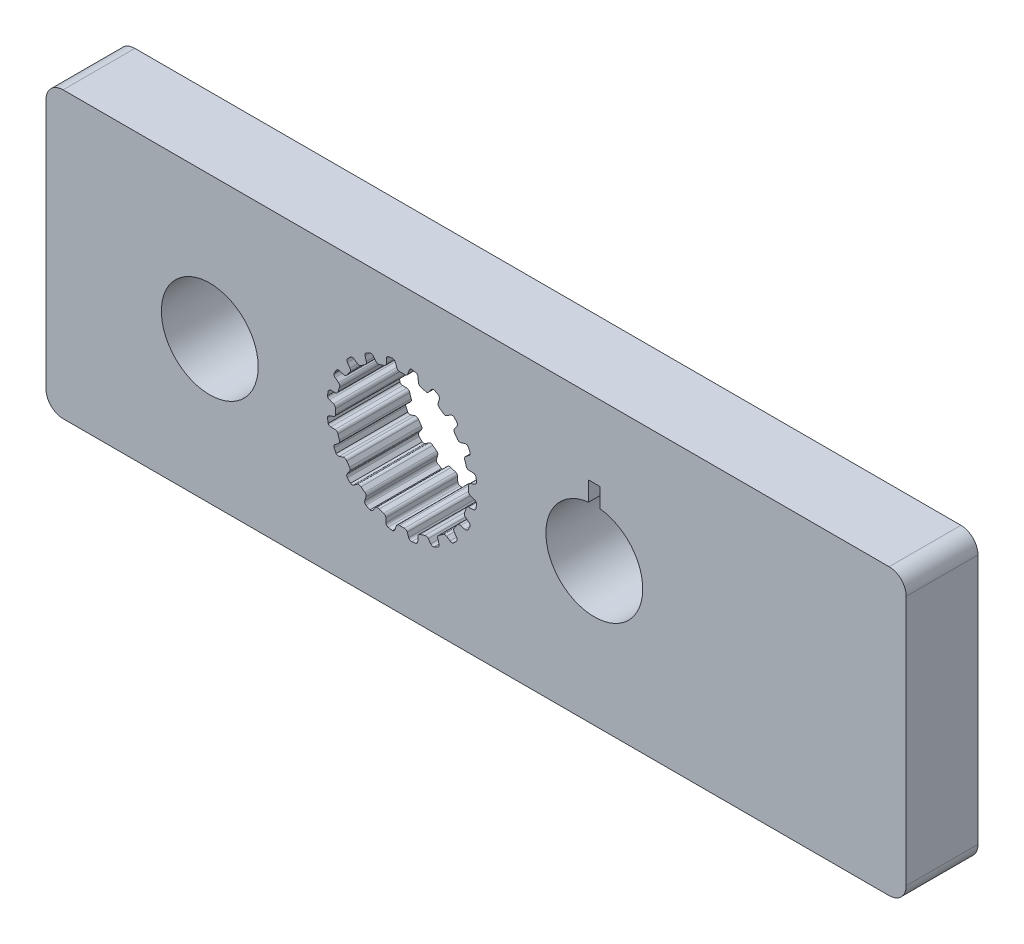
SolidWorks part; units mm, degrees
ref_plane "Front Plane" through (0, 0, 0) normal (0, 0, 1) x (1, 0, 0)
ref_plane "Top Plane" through (0, 0, 0) normal (0, 1, 0) x (1, 0, 0)
ref_plane "Right Plane" through (0, 0, 0) normal (1, 0, 0) x (0, 0, -1)
sketch "Sketch1" plane through (0, 0, 0) normal (0, 0, 1) x (1, 0, 0)
  line L0 (-0.1069, 2.9699) -> (0.1069, 2.9699)
  line L1 (0.3159, 3.2375) -> (0.2537, 3.0575)
  line L2 (-0.2964, 3.2367) -> (-0.2318, 3.0575)
  line L3 (-0.2964, 3.2367) -> (0.3159, 3.2375) construction
  line L4 (0, 3.3252) -> (0, 0) construction
  line L5 (-0.2318, 3.0575) -> (0.2537, 3.0575) construction
  line L6 (-0.4281, 3.3241) -> (0.4281, 3.3263) construction
  line L7 (0.7183, 3.1698) -> (0.7244, 2.9795)
  line L8 (0.816, 2.8576) -> (1.0195, 2.7915)
  line L9 (1.3009, 2.9815) -> (1.1862, 2.8295)
  line L10 (1.6627, 2.7927) -> (1.6097, 2.6099)
  line L11 (1.6591, 2.4655) -> (1.8322, 2.3398)
  line L12 (2.1585, 2.4335) -> (2.0025, 2.3245)
  line L13 (2.4443, 2.1423) -> (2.3374, 1.9847)
  line L14 (2.3398, 1.8322) -> (2.4655, 1.6591)
  line L15 (2.8049, 1.6474) -> (2.6228, 1.5919)
  line L16 (2.9866, 1.2821) -> (2.8363, 1.1653)
  line L17 (2.7915, 1.0195) -> (2.8576, 0.816)
  line L18 (3.1767, 0.7) -> (2.9863, 0.7035)
  line L19 (3.2367, 0.2964) -> (3.0575, 0.2318)
  line L20 (2.9699, 0.1069) -> (2.9699, -0.1069)
  line L21 (3.2375, -0.3159) -> (3.0575, -0.2537)
  line L22 (3.1698, -0.7183) -> (2.9795, -0.7244)
  line L23 (2.8576, -0.816) -> (2.7915, -1.0195)
  line L24 (2.9815, -1.3009) -> (2.8295, -1.1862)
  line L25 (2.7927, -1.6627) -> (2.6099, -1.6097)
  line L26 (2.4655, -1.6591) -> (2.3398, -1.8322)
  line L27 (2.4335, -2.1585) -> (2.3245, -2.0025)
  line L28 (2.1423, -2.4443) -> (1.9847, -2.3374)
  line L29 (1.8322, -2.3398) -> (1.6591, -2.4655)
  line L30 (1.6474, -2.8049) -> (1.5919, -2.6228)
  line L31 (1.2821, -2.9866) -> (1.1653, -2.8363)
  line L32 (1.0195, -2.7915) -> (0.816, -2.8576)
  line L33 (0.7, -3.1767) -> (0.7035, -2.9863)
  line L34 (0.2964, -3.2367) -> (0.2318, -3.0575)
  line L35 (0.1069, -2.9699) -> (-0.1069, -2.9699)
  line L36 (-0.3159, -3.2375) -> (-0.2537, -3.0575)
  line L37 (-0.7183, -3.1698) -> (-0.7244, -2.9795)
  line L38 (-0.816, -2.8576) -> (-1.0195, -2.7915)
  line L39 (-1.3009, -2.9815) -> (-1.1862, -2.8295)
  line L40 (-1.6627, -2.7927) -> (-1.6097, -2.6099)
  line L41 (-1.6591, -2.4655) -> (-1.8322, -2.3398)
  line L42 (-2.1585, -2.4335) -> (-2.0025, -2.3245)
  line L43 (-2.4443, -2.1423) -> (-2.3374, -1.9847)
  line L44 (-2.3398, -1.8322) -> (-2.4655, -1.6591)
  line L45 (-2.8049, -1.6474) -> (-2.6228, -1.5919)
  line L46 (-2.9866, -1.2821) -> (-2.8363, -1.1653)
  line L47 (-2.7915, -1.0195) -> (-2.8576, -0.816)
  line L48 (-3.1767, -0.7) -> (-2.9863, -0.7035)
  line L49 (-3.2367, -0.2964) -> (-3.0575, -0.2318)
  line L50 (-2.9699, -0.1069) -> (-2.9699, 0.1069)
  line L51 (-3.2375, 0.3159) -> (-3.0575, 0.2537)
  line L52 (-3.1698, 0.7183) -> (-2.9795, 0.7244)
  line L53 (-2.8576, 0.816) -> (-2.7915, 1.0195)
  line L54 (-2.9815, 1.3009) -> (-2.8295, 1.1862)
  line L55 (-2.7927, 1.6627) -> (-2.6099, 1.6097)
  line L56 (-2.4655, 1.6591) -> (-2.3398, 1.8322)
  line L57 (-2.4335, 2.1585) -> (-2.3245, 2.0025)
  line L58 (-2.1423, 2.4443) -> (-1.9847, 2.3374)
  line L59 (-1.8322, 2.3398) -> (-1.6591, 2.4655)
  line L60 (-1.6474, 2.8049) -> (-1.5919, 2.6228)
  line L61 (-1.2821, 2.9866) -> (-1.1653, 2.8363)
  line L62 (-1.0195, 2.7915) -> (-0.816, 2.8576)
  line L63 (-0.7, 3.1767) -> (-0.7035, 2.9863)
  line L64 (0.4281, 3.3263) -> (0.62, 3.2938)
  line L65 (1.4351, 3.0312) -> (1.6075, 2.9409)
  line L66 (2.3015, 2.4394) -> (2.4376, 2.3003)
  line L67 (2.9427, 1.6088) -> (3.0291, 1.4344)
  line L68 (3.2958, 0.6207) -> (3.3241, 0.4281)
  line L69 (3.3263, -0.4281) -> (3.2938, -0.62)
  line L70 (3.0312, -1.4351) -> (2.9409, -1.6075)
  line L71 (2.4394, -2.3015) -> (2.3003, -2.4376)
  line L72 (1.6088, -2.9427) -> (1.4344, -3.0291)
  line L73 (0.6207, -3.2958) -> (0.4281, -3.3241)
  line L74 (-0.4281, -3.3263) -> (-0.62, -3.2938)
  line L75 (-1.4351, -3.0312) -> (-1.6075, -2.9409)
  line L76 (-2.3015, -2.4394) -> (-2.4376, -2.3003)
  line L77 (-2.9427, -1.6088) -> (-3.0291, -1.4344)
  line L78 (-3.2958, -0.6207) -> (-3.3241, -0.4281)
  line L79 (-3.3263, 0.4281) -> (-3.2938, 0.62)
  line L80 (-3.0312, 1.4351) -> (-2.9409, 1.6075)
  line L81 (-2.4394, 2.3015) -> (-2.3003, 2.4376)
  line L82 (-1.6088, 2.9427) -> (-1.4344, 3.0291)
  line L83 (-0.6207, 3.2958) -> (-0.4281, 3.3241)
  line L84 (0, 0) -> (0, -6.35) construction
  line L85 (-15.875, 6.35) -> (22.479, 6.35)
  line L86 (-15.875, 6.35) -> (-15.875, -6.35)
  line L87 (-15.875, -6.35) -> (22.479, -6.35)
  line L88 (22.479, 6.35) -> (22.479, -6.35)
  line L89 (-8.5725, 0) -> (8.5725, 0) construction
  arc A0 (0.2537, 3.0575) -> (0.1069, 2.9699) centre (0.1283, 3.1009) cw
  arc A1 (-0.2318, 3.0575) -> (-0.1069, 2.9699) centre (-0.1069, 3.1026) ccw
  arc A2 (0.62, 3.2938) -> (0.7183, 3.1698) centre (0.5856, 3.1656) cw
  arc A3 (0.7244, 2.9795) -> (0.816, 2.8576) centre (0.857, 2.9838) ccw
  arc A4 (-0.4281, 3.3241) -> (-0.2964, 3.2367) centre (-0.4213, 3.1916) cw
  arc A5 (0.4281, 3.3263) -> (0.3159, 3.2375) centre (0.4413, 3.1942) ccw
  arc A6 (1.1862, 2.8295) -> (1.0195, 2.7915) centre (1.0802, 2.9095) cw
  arc A7 (1.4351, 3.0312) -> (1.3009, 2.9815) centre (1.4068, 2.9015) ccw
  arc A8 (1.6075, 2.9409) -> (1.6627, 2.7927) centre (1.5352, 2.8297) cw
  arc A9 (1.6097, 2.6099) -> (1.6591, 2.4655) centre (1.7371, 2.5729) ccw
  arc A10 (2.0025, 2.3245) -> (1.8322, 2.3398) centre (1.9264, 2.4332) cw
  arc A11 (2.3015, 2.4394) -> (2.1585, 2.4335) centre (2.2346, 2.3248) ccw
  arc A12 (2.4376, 2.3003) -> (2.4443, 2.1423) centre (2.3345, 2.2168) cw
  arc A13 (2.3374, 1.9847) -> (2.3398, 1.8322) centre (2.4472, 1.9102) ccw
  arc A14 (2.6228, 1.5919) -> (2.4655, 1.6591) centre (2.5841, 1.7189) cw
  arc A15 (2.9427, 1.6088) -> (2.8049, 1.6474) centre (2.8436, 1.5205) ccw
  arc A16 (3.0291, 1.4344) -> (2.9866, 1.2821) centre (2.9052, 1.3869) cw
  arc A17 (2.8363, 1.1653) -> (2.7915, 1.0195) centre (2.9177, 1.0605) ccw
  arc A18 (2.9863, 0.7035) -> (2.8576, 0.816) centre (2.9887, 0.8362) cw
  arc A19 (3.2958, 0.6207) -> (3.1767, 0.7) centre (3.1743, 0.5673) ccw
  arc A20 (3.3241, 0.4281) -> (3.2367, 0.2964) centre (3.1916, 0.4213) cw
  arc A21 (3.0575, 0.2318) -> (2.9699, 0.1069) centre (3.1026, 0.1069) ccw
  arc A22 (3.0575, -0.2537) -> (2.9699, -0.1069) centre (3.1009, -0.1283) cw
  arc A23 (3.3263, -0.4281) -> (3.2375, -0.3159) centre (3.1942, -0.4413) ccw
  arc A24 (3.2938, -0.62) -> (3.1698, -0.7183) centre (3.1656, -0.5856) cw
  arc A25 (2.9795, -0.7244) -> (2.8576, -0.816) centre (2.9838, -0.857) ccw
  arc A26 (2.8295, -1.1862) -> (2.7915, -1.0195) centre (2.9095, -1.0802) cw
  arc A27 (3.0312, -1.4351) -> (2.9815, -1.3009) centre (2.9015, -1.4068) ccw
  arc A28 (2.9409, -1.6075) -> (2.7927, -1.6627) centre (2.8297, -1.5352) cw
  arc A29 (2.6099, -1.6097) -> (2.4655, -1.6591) centre (2.5729, -1.7371) ccw
  arc A30 (2.3245, -2.0025) -> (2.3398, -1.8322) centre (2.4332, -1.9264) cw
  arc A31 (2.4394, -2.3015) -> (2.4335, -2.1585) centre (2.3248, -2.2346) ccw
  arc A32 (2.3003, -2.4376) -> (2.1423, -2.4443) centre (2.2168, -2.3345) cw
  arc A33 (1.9847, -2.3374) -> (1.8322, -2.3398) centre (1.9102, -2.4472) ccw
  arc A34 (1.5919, -2.6228) -> (1.6591, -2.4655) centre (1.7189, -2.5841) cw
  arc A35 (1.6088, -2.9427) -> (1.6474, -2.8049) centre (1.5205, -2.8436) ccw
  arc A36 (1.4344, -3.0291) -> (1.2821, -2.9866) centre (1.3869, -2.9052) cw
  arc A37 (1.1653, -2.8363) -> (1.0195, -2.7915) centre (1.0605, -2.9177) ccw
  arc A38 (0.7035, -2.9863) -> (0.816, -2.8576) centre (0.8362, -2.9887) cw
  arc A39 (0.6207, -3.2958) -> (0.7, -3.1767) centre (0.5673, -3.1743) ccw
  arc A40 (0.4281, -3.3241) -> (0.2964, -3.2367) centre (0.4213, -3.1916) cw
  arc A41 (0.2318, -3.0575) -> (0.1069, -2.9699) centre (0.1069, -3.1026) ccw
  arc A42 (-0.2537, -3.0575) -> (-0.1069, -2.9699) centre (-0.1283, -3.1009) cw
  arc A43 (-0.4281, -3.3263) -> (-0.3159, -3.2375) centre (-0.4413, -3.1942) ccw
  arc A44 (-0.62, -3.2938) -> (-0.7183, -3.1698) centre (-0.5856, -3.1656) cw
  arc A45 (-0.7244, -2.9795) -> (-0.816, -2.8576) centre (-0.857, -2.9838) ccw
  arc A46 (-1.1862, -2.8295) -> (-1.0195, -2.7915) centre (-1.0802, -2.9095) cw
  arc A47 (-1.4351, -3.0312) -> (-1.3009, -2.9815) centre (-1.4068, -2.9015) ccw
  arc A48 (-1.6075, -2.9409) -> (-1.6627, -2.7927) centre (-1.5352, -2.8297) cw
  arc A49 (-1.6097, -2.6099) -> (-1.6591, -2.4655) centre (-1.7371, -2.5729) ccw
  arc A50 (-2.0025, -2.3245) -> (-1.8322, -2.3398) centre (-1.9264, -2.4332) cw
  arc A51 (-2.3015, -2.4394) -> (-2.1585, -2.4335) centre (-2.2346, -2.3248) ccw
  arc A52 (-2.4376, -2.3003) -> (-2.4443, -2.1423) centre (-2.3345, -2.2168) cw
  arc A53 (-2.3374, -1.9847) -> (-2.3398, -1.8322) centre (-2.4472, -1.9102) ccw
  arc A54 (-2.6228, -1.5919) -> (-2.4655, -1.6591) centre (-2.5841, -1.7189) cw
  arc A55 (-2.9427, -1.6088) -> (-2.8049, -1.6474) centre (-2.8436, -1.5205) ccw
  arc A56 (-3.0291, -1.4344) -> (-2.9866, -1.2821) centre (-2.9052, -1.3869) cw
  arc A57 (-2.8363, -1.1653) -> (-2.7915, -1.0195) centre (-2.9177, -1.0605) ccw
  arc A58 (-2.9863, -0.7035) -> (-2.8576, -0.816) centre (-2.9887, -0.8362) cw
  arc A59 (-3.2958, -0.6207) -> (-3.1767, -0.7) centre (-3.1743, -0.5673) ccw
  arc A60 (-3.3241, -0.4281) -> (-3.2367, -0.2964) centre (-3.1916, -0.4213) cw
  arc A61 (-3.0575, -0.2318) -> (-2.9699, -0.1069) centre (-3.1026, -0.1069) ccw
  arc A62 (-3.0575, 0.2537) -> (-2.9699, 0.1069) centre (-3.1009, 0.1283) cw
  arc A63 (-3.3263, 0.4281) -> (-3.2375, 0.3159) centre (-3.1942, 0.4413) ccw
  arc A64 (-3.2938, 0.62) -> (-3.1698, 0.7183) centre (-3.1656, 0.5856) cw
  arc A65 (-2.9795, 0.7244) -> (-2.8576, 0.816) centre (-2.9838, 0.857) ccw
  arc A66 (-2.8295, 1.1862) -> (-2.7915, 1.0195) centre (-2.9095, 1.0802) cw
  arc A67 (-3.0312, 1.4351) -> (-2.9815, 1.3009) centre (-2.9015, 1.4068) ccw
  arc A68 (-2.9409, 1.6075) -> (-2.7927, 1.6627) centre (-2.8297, 1.5352) cw
  arc A69 (-2.6099, 1.6097) -> (-2.4655, 1.6591) centre (-2.5729, 1.7371) ccw
  arc A70 (-2.3245, 2.0025) -> (-2.3398, 1.8322) centre (-2.4332, 1.9264) cw
  arc A71 (-2.4394, 2.3015) -> (-2.4335, 2.1585) centre (-2.3248, 2.2346) ccw
  arc A72 (-2.3003, 2.4376) -> (-2.1423, 2.4443) centre (-2.2168, 2.3345) cw
  arc A73 (-1.9847, 2.3374) -> (-1.8322, 2.3398) centre (-1.9102, 2.4472) ccw
  arc A74 (-1.5919, 2.6228) -> (-1.6591, 2.4655) centre (-1.7189, 2.5841) cw
  arc A75 (-1.6088, 2.9427) -> (-1.6474, 2.8049) centre (-1.5205, 2.8436) ccw
  arc A76 (-1.4344, 3.0291) -> (-1.2821, 2.9866) centre (-1.3869, 2.9052) cw
  arc A77 (-1.1653, 2.8363) -> (-1.0195, 2.7915) centre (-1.0605, 2.9177) ccw
  arc A78 (-0.7035, 2.9863) -> (-0.816, 2.8576) centre (-0.8362, 2.9887) cw
  arc A79 (-0.6207, 3.2958) -> (-0.7, 3.1767) centre (-0.5673, 3.1743) ccw
  circle A80 centre (0, 0) radius 12.7 construction
  circle A81 centre (0, 0) radius 5.08 construction
  circle A82 centre (-8.5725, 0) radius 2.159
  circle A83 centre (8.5725, 0) radius 2.159
  point P14 (0, 2.9699)
  point P247 (0, 0)
  dimension "D4" = 0.1327
  dimension "D8" = 20
  dimension "D9" = 25.4
  dimension "D13" = 10.16
  dimension "D16" = 4.318
  dimension "D1" = 2.9699
  dimension "D2" = 0.2139
  dimension "D3" = 0.1904
  dimension "D5" = 0.0877
  dimension "D6" = 0.4855
  dimension "D7" = 0.8563
  dimension "D10" = 12.7
  dimension "D11" = 38.354
  dimension "D12" = 6.35
  dimension "D14" = 15.875
  dimension "D15" = 17.145
extrude "Boss-Extrude1" add sketch "Sketch1" along normal mid plane 3.2004
sketch "Sketch2" plane through (0, 0, 1.6002) normal (0, 0, 1) x (1, 0, 0)
  line L0 (8.5725, 1.7323) -> (8.5725, 0) construction
  line L1 (8.3185, 3.0023) -> (8.8265, 3.0023)
  line L2 (8.3185, 3.0023) -> (8.3185, 1.7323)
  line L3 (8.3185, 1.7323) -> (8.8265, 1.7323)
  line L4 (8.8265, 3.0023) -> (8.8265, 1.7323)
  line L5 (22.479, 6.35) -> (-15.875, 6.35) construction
  circle A1 centre (8.5725, 0) radius 2.159 construction
  point P10 (0, 0)
  dimension "D1" = 1.7323
  dimension "D2" = 0.508
  dimension "D3" = 1.27
extrude "Cut-Extrude1" cut sketch "Sketch2" against normal up to surface (3.2004 mm away) up to face at (3.302, 0, -1.6002)
fillet "Fillet1" radius 0.762 4 edges at (22.479, -6.35, 0) (22.479, 6.35, 0) (-15.875, -6.35, 0) (-15.875, 6.35, 0)
